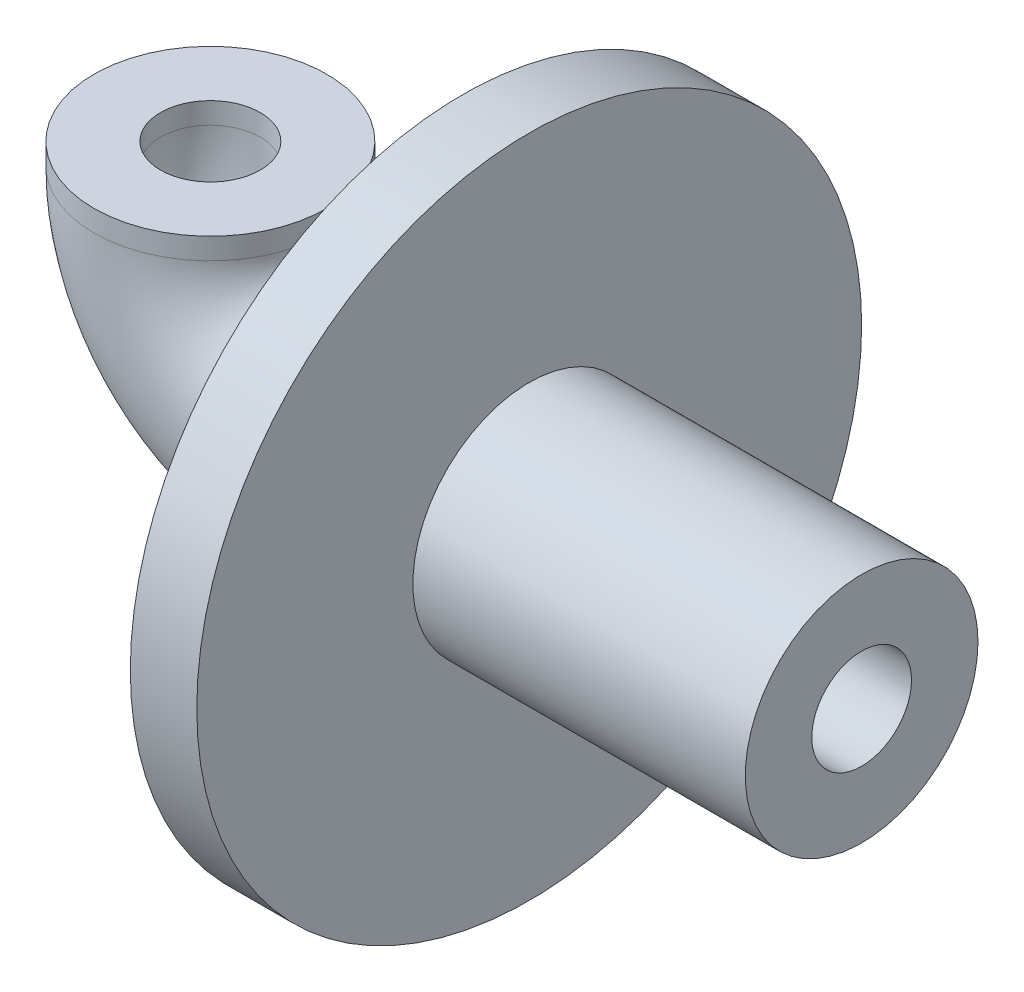
SolidWorks part; units mm, degrees
ref_plane "Front Plane" through (0, 0, 0) normal (0, 0, 1) x (1, 0, 0)
ref_plane "Top Plane" through (0, 0, 0) normal (0, 1, 0) x (1, 0, 0)
ref_plane "Right Plane" through (0, 0, 0) normal (1, 0, 0) x (0, 0, -1)
sketch "Sketch1" plane through (0, 0, 0) normal (1, 0, 0) x (0, 0, -1)
  circle A0 centre (0, 0) radius 5
  dimension "D1" = 10
extrude "Boss-Extrude1" add sketch "Sketch1" along normal blind 1
sketch "Sketch2" plane through (1, 0, 0) normal (1, 0, 0) x (0, 0, -1)
  circle A0 centre (0, 0) radius 0.75
  circle A1 centre (0, 0) radius 1.75
  dimension "D1" = 1.5
  dimension "D2" = 1
extrude "Boss-Extrude2" add sketch "Sketch2" along normal blind 5
sketch "Sketch4" plane through (0, 0, 0) normal (-1, 0, 0) x (0, 0, 1)
  circle A1 centre (0, 0) radius 1.75
  circle A2 centre (0, 0) radius 1.75
  circle A3 centre (0, 0) radius 0.75
  circle A4 centre (0, 0) radius 0.75
  dimension "D1" = 0
  dimension "D2" = 0
extrude "Cut-Extrude1" cut sketch "Sketch4" against normal blind 10 contours A4
sketch "Sketch5" plane through (0, 0, 0) normal (-1, 0, 0) x (0, 0, 1)
  circle A1 centre (0, 0) radius 1.75
  circle A2 centre (0, 0) radius 1.75
  circle A3 centre (0, 0) radius 0.75
  circle A4 centre (0, 0) radius 0.75
  dimension "D1" = 0
  dimension "D2" = 0
sketch "Sketch6" plane through (0, 0, 0) normal (0, 0, 1) x (1, 0, 0)
  line L0 (0, 1.75) -> (-1.6232, 1.75)
  line L1 (0, 1.75) -> (0, -1.75) construction
  line L2 (0, -5) -> (0, 5) construction
  line L3 (-2.0455, 2.1724) -> (-2.0455, 2.4927)
  arc A0 (-1.6232, 1.75) -> (-2.0455, 2.1724) centre (-1.6232, 2.1724) cw
sketch "Sketch7" plane through (0, 0, 0) normal (-1, 0, 0) x (0, 0, 1)
  circle A1 centre (0, 0) radius 0.75
  circle A2 centre (0, 0) radius 0.75
  circle A3 centre (0, 0) radius 1.75
  circle A4 centre (0, 0) radius 1.75
  dimension "D1" = 0
  dimension "D2" = 0
sweep "Sweep5" add profiles "Sketch5" path "Sketch6"
